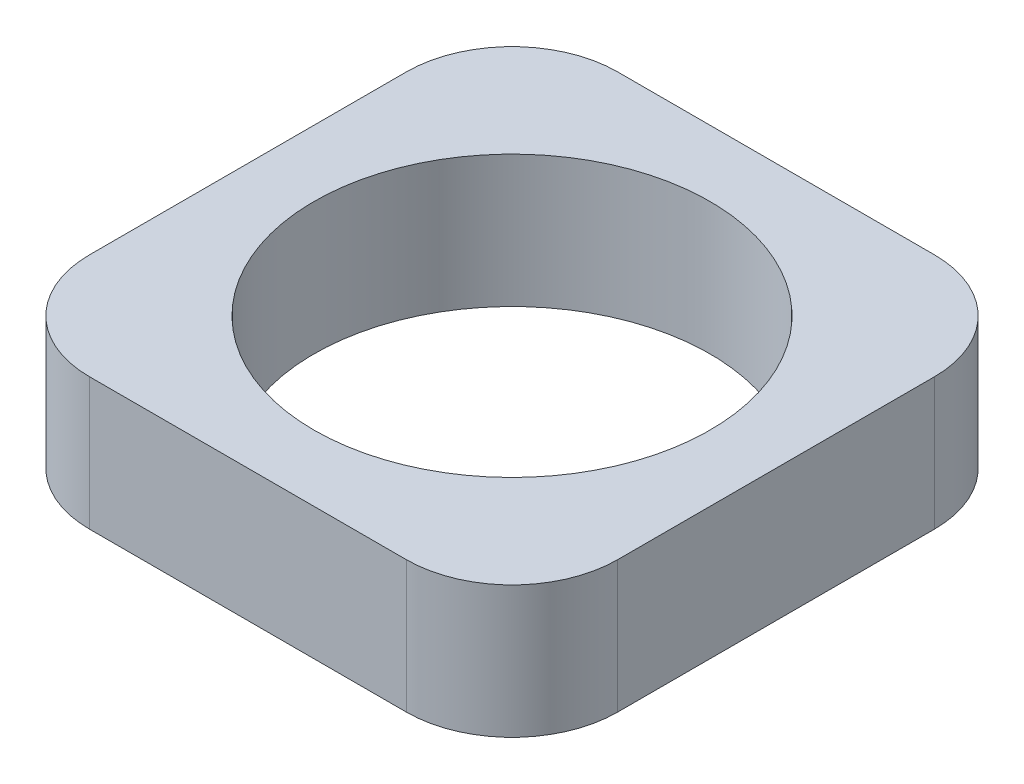
SolidWorks part; units mm, degrees
ref_plane "Alzado" through (0, 0, 0) normal (0, 0, 1) x (1, 0, 0)
ref_plane "Planta" through (0, 0, 0) normal (0, 1, 0) x (1, 0, 0)
ref_plane "Vista lateral" through (0, 0, 0) normal (1, 0, 0) x (0, 0, -1)
sketch "Croquis1" plane through (0, 0, 0) normal (0, 1, 0) x (1, 0, 0)
  line L1 (-6, -10) -> (6, -10)
  line L2 (-10, -6) -> (-10, 6)
  line L3 (-6, 10) -> (6, 10)
  line L4 (10, -6) -> (10, 6)
  line L5 (-10, -10) -> (10, 10) construction
  line L6 (-10, 10) -> (10, -10) construction
  arc A0 (-10, -6) -> (-6, -10) centre (-6, -6) ccw
  arc A1 (10, -6) -> (6, -10) centre (6, -6) cw
  arc A2 (10, 6) -> (6, 10) centre (6, 6) ccw
  arc A3 (-10, 6) -> (-6, 10) centre (-6, 6) cw
  point P0 (0, 0)
  dimension "D3" = 4
  dimension "D1" = 20
  dimension "D2" = 20
extrude "Saliente-Extruir1" add sketch "Croquis1" along normal blind 5
sketch "Croquis2" plane through (0, 5, 0) normal (0, 1, 0) x (1, 0, 0)
  circle A0 centre (0, 0) radius 7.5
  dimension "D1" = 15
extrude "Cortar-Extruir1" cut sketch "Croquis2" against normal through all
